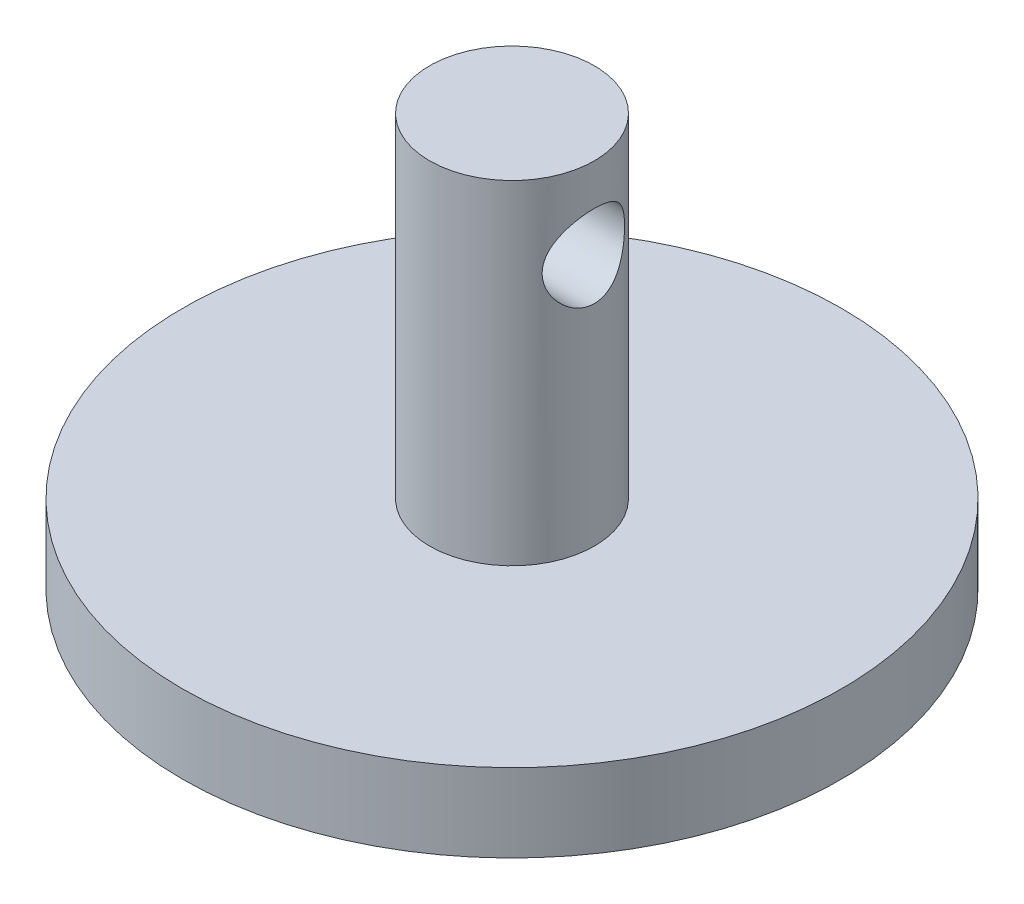
SolidWorks part; units mm, degrees
ref_plane "Front Plane" through (0, 0, 0) normal (0, 0, 1) x (1, 0, 0)
ref_plane "Top Plane" through (0, 0, 0) normal (0, 1, 0) x (1, 0, 0)
ref_plane "Right Plane" through (0, 0, 0) normal (1, 0, 0) x (0, 0, -1)
sketch "Sketch1" plane through (0, 0, 0) normal (1, 0, 0) x (0, 0, -1)
  line L0 (0, 0) -> (-8, 0)
  line L1 (-8, 0) -> (-8, 1.9)
  line L2 (-8, 1.9) -> (-2, 1.9)
  line L3 (-2, 1.9) -> (-2, 10)
  line L4 (-2, 10) -> (0, 10)
  line L5 (0, 10) -> (0, 0)
  point P7 (-1.6086, 1.3282)
  point P8 (-1.1944, 0.9898)
  dimension "D1" = 8
  dimension "D2" = 2
  dimension "D3" = 1.9
  dimension "D4" = 10
revolve "Revolve1" add sketch "Sketch1" angle 360 about L5
sketch "Sketch2" plane through (0, 0, 0) normal (1, 0, 0) x (0, 0, -1)
  circle A0 centre (0, 8) radius 1
  dimension "D1" = 2
  dimension "D2" = 8
extrude "Cut-Extrude1" cut sketch "Sketch2" against normal through all both and the other way through all
sketch "Sketch3" plane through (0, 10, 0) normal (0, 1, 0) x (1, 0, 0)
  point P0 (0, 0)
  point P1 (0, 0)
